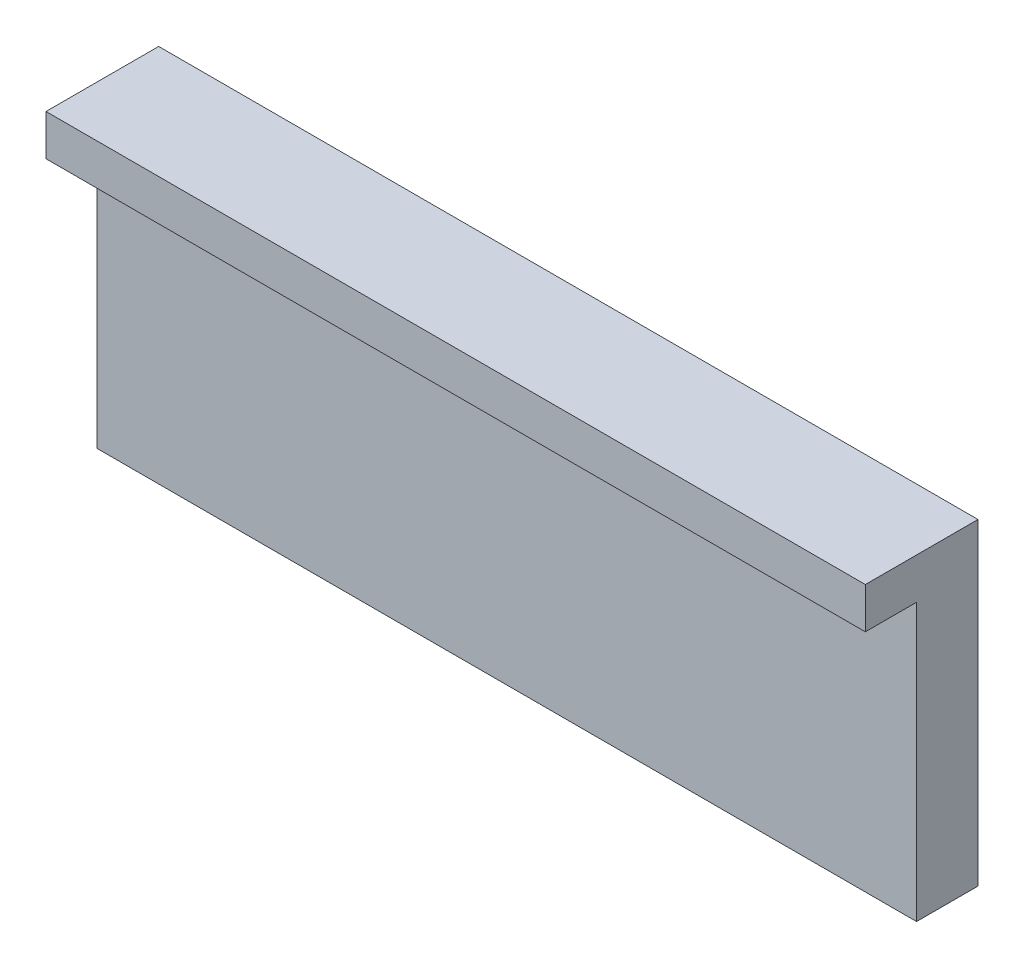
SolidWorks part; units mm, degrees
ref_plane "Alzado" through (0, 0, 0) normal (0, 0, 1) x (1, 0, 0)
ref_plane "Planta" through (0, 0, 0) normal (0, 1, 0) x (1, 0, 0)
ref_plane "Vista lateral" through (0, 0, 0) normal (1, 0, 0) x (0, 0, -1)
sketch "Croquis1" plane through (0, 0, 0) normal (0, 0, 1) x (1, 0, 0)
  line L1 (80, 31) -> (0, 31)
  line L2 (80, 31) -> (80, 0)
  line L3 (80, 0) -> (0, 0)
  line L4 (0, 31) -> (0, 0)
  dimension "D1" = 31
  dimension "D2" = 80
extrude "Saliente-Extruir1" add sketch "Croquis1" along normal blind 6
sketch "Croquis2" plane through (0, 0, 6) normal (0, 0, 1) x (1, 0, 0)
  line L0 (80, 0) -> (80, 31) construction
  line L1 (0, 31) -> (80, 31)
  line L2 (0, 31) -> (0, 27)
  line L3 (0, 27) -> (80, 27)
  line L4 (80, 31) -> (80, 27)
  dimension "D1" = 4
extrude "Saliente-Extruir2" add sketch "Croquis2" along normal blind 5
